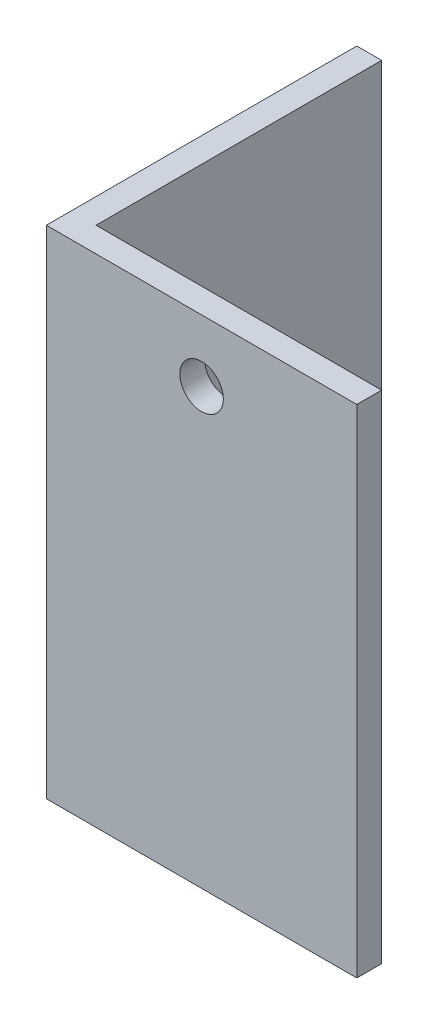
SolidWorks part; units mm, degrees
ref_plane "Front Plane" through (0, 0, 0) normal (0, 0, 1) x (1, 0, 0)
ref_plane "Top Plane" through (0, 0, 0) normal (0, 1, 0) x (1, 0, 0)
ref_plane "Right Plane" through (0, 0, 0) normal (1, 0, 0) x (0, 0, -1)
sketch "Sketch1" plane through (0, 0, 0) normal (0, 1, 0) x (1, 0, 0)
  line L1 (0, 0) -> (25, 0)
  line L2 (0, 0) -> (0, 25)
  line L3 (0, 25) -> (2, 25)
  line L4 (25, 0) -> (25, 2)
  line L7 (25, 2) -> (2, 2)
  line L8 (2, 25) -> (2, 2)
  dimension "D1" = 25
  dimension "D2" = 25
  dimension "D3" = 2
  dimension "D4" = 2
extrude "Boss-Extrude1" add sketch "Sketch1" along normal blind 40
sketch "Sketch2" plane through (0, 0, 0) normal (1, 0, 0) x (0, 0, -1)
  line L3 (0, 40) -> (0, 0) construction
  line L4 (25, 0) -> (0, 0) construction
  circle A1 centre (10, 5) radius 1.75
  dimension "D1" = 3.5
  dimension "D2" = 10
  dimension "D3" = 5
extrude "Cut-Extrude1" cut sketch "Sketch2" along normal blind 50
sketch "Sketch3" plane through (0, 0, 0) normal (0, 0, -1) x (-1, 0, 0)
  line L3 (0, 40) -> (0, 0) construction
  line L4 (0, 0) -> (-25, 0) construction
  circle A0 centre (-12.5, 35) radius 1.75
  dimension "D1" = 12.5
  dimension "D2" = 3.5
  dimension "D3" = 35
extrude "Cut-Extrude2" cut sketch "Sketch3" along normal blind 50
